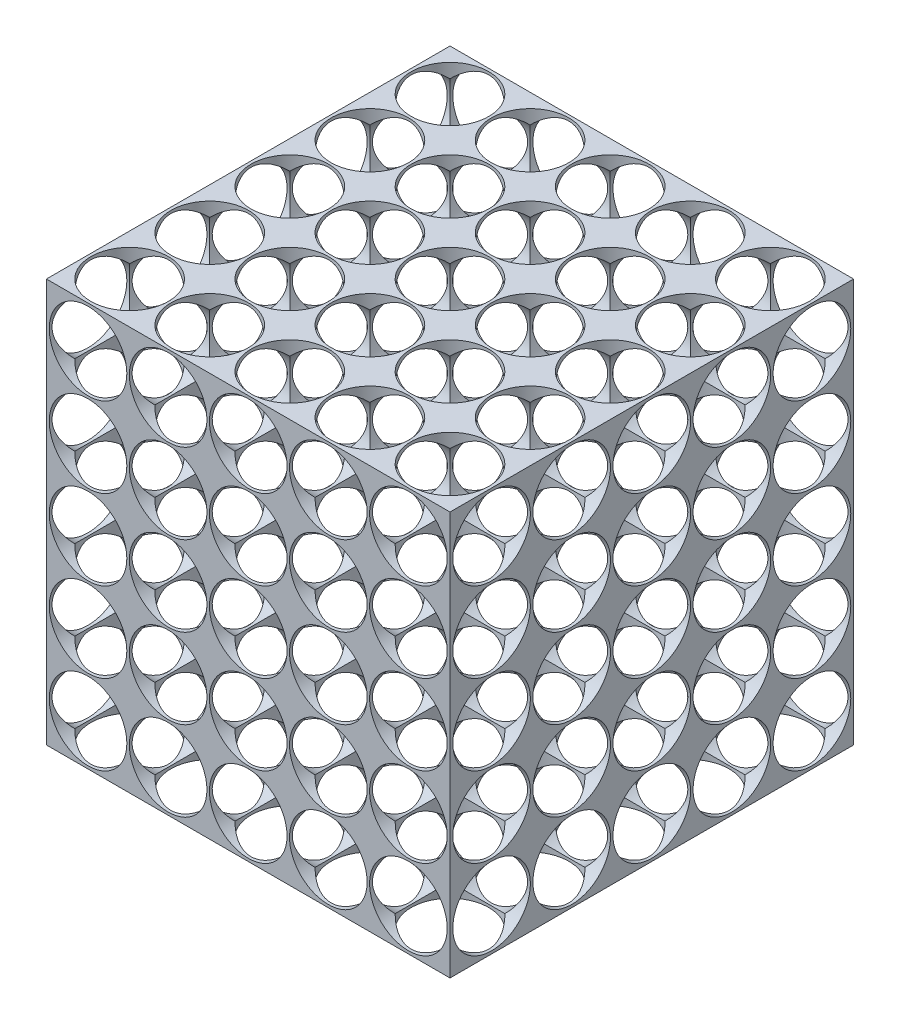
SolidWorks part; units mm, degrees
material "6061 Alloy"
ref_plane "Front Plane" through (0, 0, 0) normal (0, 0, 1) x (1, 0, 0)
ref_plane "Top Plane" through (0, 0, 0) normal (0, 1, 0) x (1, 0, 0)
ref_plane "Right Plane" through (0, 0, 0) normal (1, 0, 0) x (0, 0, -1)
sketch "Sketch1" plane through (0, 0, 0) normal (0, 1, 0) x (1, 0, 0)
  line L1 (0, 0) -> (82.55, 0)
  line L2 (0, 0) -> (0, 82.55)
  line L3 (0, 82.55) -> (82.55, 82.55)
  line L4 (82.55, 0) -> (82.55, 82.55)
  dimension "D1" = 82.55
extrude "Boss-Extrude1" add sketch "Sketch1" along normal blind 82.55
hole_wizard "5/8 (0.625) Diameter Hole1" positions "Sketch2" profile "Sketch3" hole size "5/8" standard "ANSI Inch" end condition through all
sketch "Sketch2" plane through (0, 82.55, 0) normal (0, 1, 0) x (1, 0, 0)
  line L0 (0, 0) -> (82.55, 0) construction
  line L1 (0, 82.55) -> (0, 0) construction
  point P0 (8.509, 8.509)
  dimension "D1" = 8.509
  dimension "D2" = 8.509
sketch "Sketch3" plane through (8.509, 82.55, -8.509) normal (1, 0, 0) x (0, 0, 1)
  line L0 (0, 0) -> (0, 82.55)
  line L1 (0, 82.55) -> (7.9375, 82.55)
  line L2 (7.9375, 82.55) -> (7.9375, 0)
  line L5 (7.9375, 0) -> (0, 0)
  line L11 (0, -6.35) -> (0, 107.95) construction
  dimension "Thru Hole Dia." = 15.875
  dimension "Thru Hole Depth" = 82.55
pattern_linear "LPattern1" count 5 spacing 16.383 along (0, 0, -1) count 5 spacing 16.383 along (1, 0, 0) of "5/8 (0.625) Diameter Hole1"
hole_wizard "5/8 (0.625) Diameter Hole2" positions "Sketch6" profile "Sketch5" hole size "5/8" standard "ANSI Inch" end condition through all
sketch "Sketch6" plane through (0, 0, 0) normal (0, 0, 1) x (1, 0, 0)
  line L0 (0, 82.55) -> (0, 0) construction
  line L1 (0, 0) -> (82.55, 0) construction
  point P0 (8.509, 8.509)
  dimension "D1" = 8.509
  dimension "D2" = 8.509
sketch "Sketch5" plane through (8.509, 8.509, 0) normal (1, 0, 0) x (0, -1, 0)
  line L0 (0, 0) -> (0, 82.55)
  line L1 (0, 82.55) -> (7.9375, 82.55)
  line L2 (7.9375, 82.55) -> (7.9375, 0)
  line L5 (7.9375, 0) -> (0, 0)
  line L11 (0, -6.35) -> (0, 107.95) construction
  dimension "Thru Hole Dia." = 15.875
  dimension "Thru Hole Depth" = 82.55
pattern_linear "LPattern3" count 5 spacing 16.383 along (0, 1, 0) count 5 spacing 16.383 along (1, 0, 0) of "5/8 (0.625) Diameter Hole2"
hole_wizard "5/8 (0.625) Diameter Hole3" positions "Sketch7" profile "Sketch8" hole size "5/8" standard "ANSI Inch" end condition through all
sketch "Sketch7" plane through (82.55, 0, 0) normal (1, 0, 0) x (0, 0, -1)
  line L0 (0, 82.55) -> (0, 0) construction
  line L1 (0, 0) -> (82.55, 0) construction
  point P0 (8.509, 8.509)
  dimension "D1" = 8.509
  dimension "D2" = 8.509
sketch "Sketch8" plane through (82.55, 8.509, -8.509) normal (0, 1, 0) x (0, 0, -1)
  line L0 (0, 0) -> (0, 82.55)
  line L1 (0, 82.55) -> (7.9375, 82.55)
  line L2 (7.9375, 82.55) -> (7.9375, 0)
  line L5 (7.9375, 0) -> (0, 0)
  line L11 (0, -6.35) -> (0, 107.95) construction
  dimension "Thru Hole Dia." = 15.875
  dimension "Thru Hole Depth" = 82.55
pattern_linear "LPattern4" count 5 spacing 16.383 along (0, 1, 0) count 5 spacing 16.383 along (0, 0, -1) of "5/8 (0.625) Diameter Hole3"
equation "\"D1\"=3.25"
equation "\"D1@Sketch1\"=\"D1\""
equation "\"D2@Sketch2\"=.3350"
